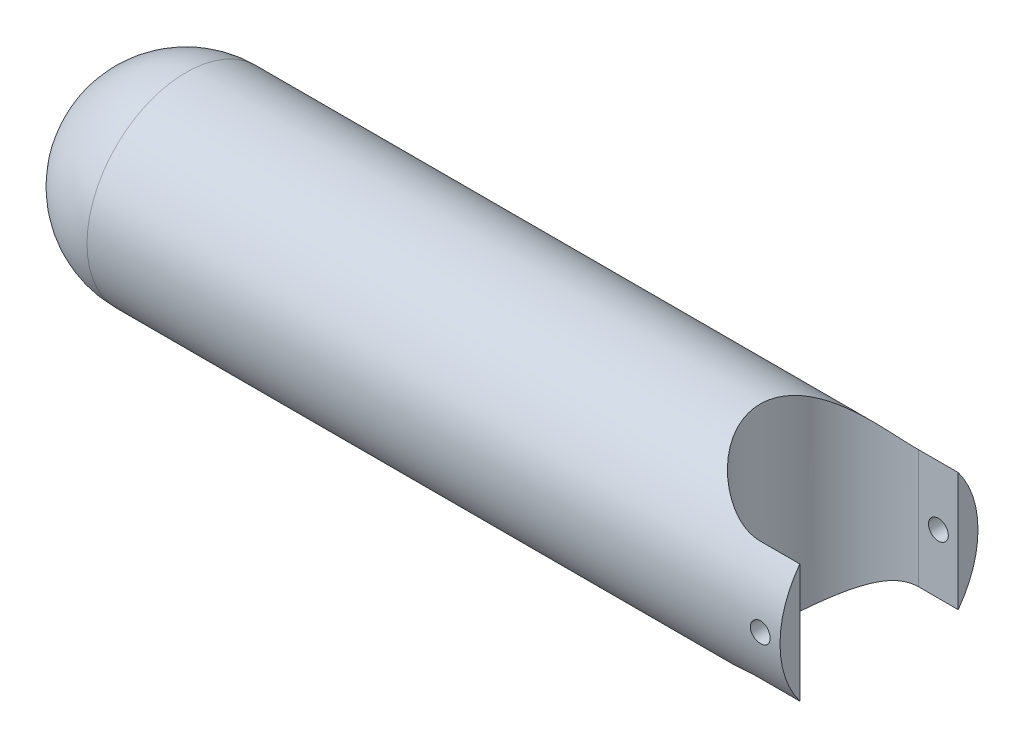
SolidWorks part; units mm, degrees
material "Aleación 2014"
ref_plane "Alzado" through (0, 0, 0) normal (0, 0, 1) x (1, 0, 0)
ref_plane "Planta" through (0, 0, 0) normal (0, 1, 0) x (1, 0, 0)
ref_plane "Vista lateral" through (0, 0, 0) normal (1, 0, 0) x (0, 0, -1)
sketch "Croquis3" plane through (0, 0, 0) normal (0, 1, 0) x (1, 0, 0)
  line L2 (-38.082, 0) -> (-19.332, 6.25) construction
  line L5 (-38.082, 0) -> (161.918, 0)
  line L17 (161.918, 0) -> (161.918, 25)
  line L19 (-13.082, 25) -> (161.918, 25)
  arc A5 (-38.082, 0) -> (-13.082, 25) centre (-13.082, 0) cw
  dimension "D2" = 175
  dimension "D1" = 200
revolve "Revolución10" add sketch "Croquis3" angle 360 about L5
sketch "Croquis6" plane through (0, 0, 0) normal (0, 0, 1) x (1, 0, 0)
  circle A4 centre (156.918, 0) radius 2.5
extrude "Cortar-Extruir1" cut sketch "Croquis6" against normal through all both and the other way through all
sketch "Croquis9" plane through (0, 0, 0) normal (0, 1, 0) x (1, 0, 0)
  line L2 (161.918, 20) -> (161.918, -20)
  line L6 (151.918, 20) -> (161.918, 20)
  line L7 (151.918, -20) -> (161.918, -20)
  arc A0 (151.918, 20) -> (151.918, -20) centre (151.918, 0) ccw
  dimension "D2" = 40
extrude "Cortar-Extruir3" cut sketch "Croquis9" against normal through all both and the other way through all contours L2 L7 A0 L6
